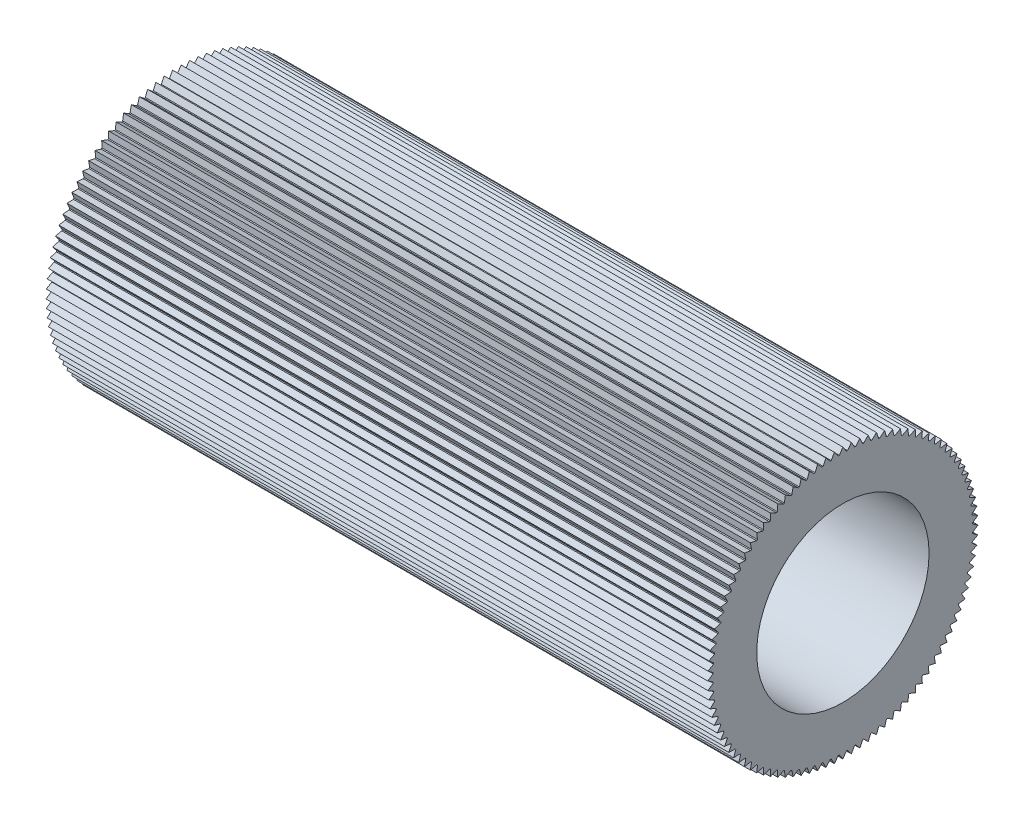
SolidWorks part; units mm, degrees
ref_plane "Front Plane" through (0, 0, 0) normal (0, 0, 1) x (1, 0, 0)
ref_plane "Top Plane" through (0, 0, 0) normal (0, 1, 0) x (1, 0, 0)
ref_plane "Right Plane" through (0, 0, 0) normal (1, 0, 0) x (0, 0, -1)
sketch "Sketch1" plane through (0, 0, 0) normal (1, 0, 0) x (0, 0, -1)
  circle A0 centre (0, 0) radius 4.7625
  circle A1 centre (0, 0) radius 3.1623
  dimension "D1" = 9.525
  dimension "D2" = 6.3246
extrude "Boss-Extrude1" add sketch "Sketch1" along normal blind 24.2824
sketch "Sketch2" plane through (0, 0, 0) normal (-1, 0, 0) x (0, 0, 1)
  line L0 (0, 0) -> (0, 6.3449) construction
  line L1 (-0.1524, 4.7288) -> (0, 4.9577)
  line L2 (0, 4.9577) -> (0.1524, 4.7288)
  line L3 (-0.1524, 4.7288) -> (0.1524, 4.7288)
  dimension "D2" = 0.1524
  dimension "D3" = 0.3048
extrude "Boss-Extrude2" add sketch "Sketch2" against normal up to surface (24.2824 mm away) up to face at (24.2824, 0, -4.7625)
pattern_circular "CirPattern3" count 100 over 360 about axis through (0, 0, 0) along (1, 0, 0) of "Boss-Extrude2", "Boss-Extrude1"
